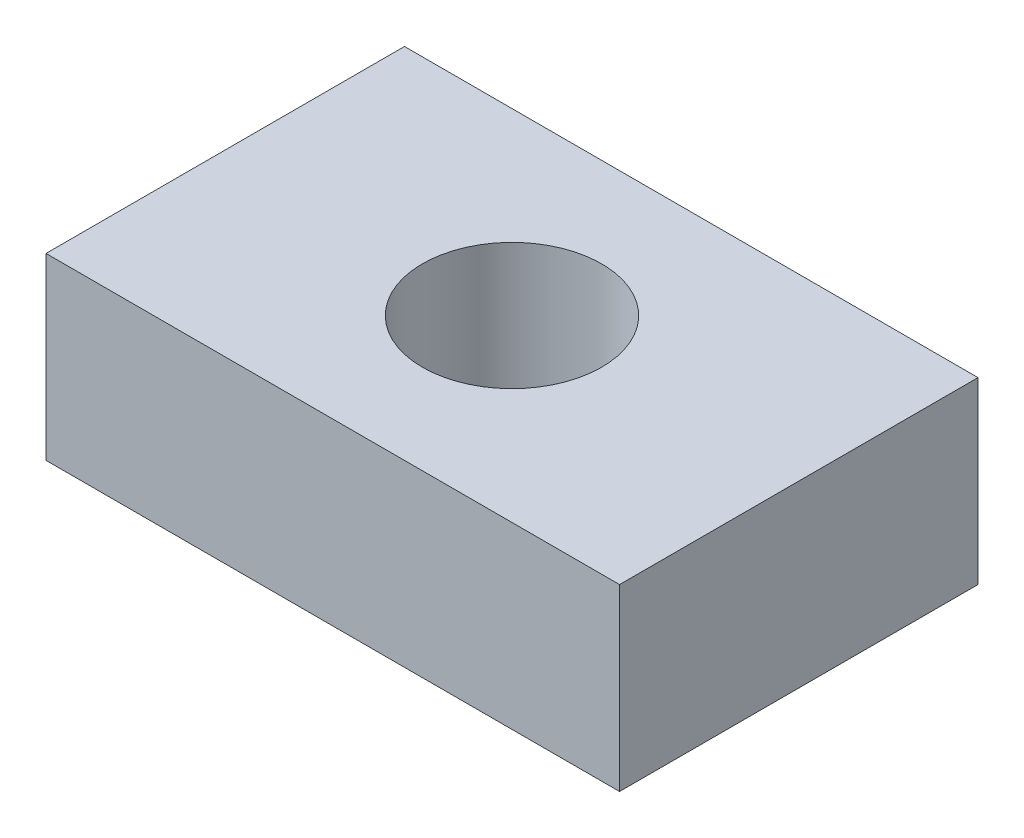
SolidWorks part; units mm, degrees
ref_plane "Front Plane" through (0, 0, 0) normal (0, 0, 1) x (1, 0, 0)
ref_plane "Top Plane" through (0, 0, 0) normal (0, 1, 0) x (1, 0, 0)
ref_plane "Right Plane" through (0, 0, 0) normal (1, 0, 0) x (0, 0, -1)
sketch "Sketch1" plane through (0, 0, 0) normal (0, 1, 0) x (1, 0, 0)
  line L1 (-80, -50) -> (80, -50)
  line L2 (-80, -50) -> (-80, 50)
  line L3 (-80, 50) -> (80, 50)
  line L4 (80, -50) -> (80, 50)
  line L5 (-80, -50) -> (80, 50) construction
  line L6 (-80, 50) -> (80, -50) construction
  circle A0 centre (0, 0) radius 25
  point P0 (0, 0)
  dimension "D3" = 50
  dimension "D1" = 160
  dimension "D2" = 100
extrude "Boss-Extrude1" add sketch "Sketch1" along normal blind 50
